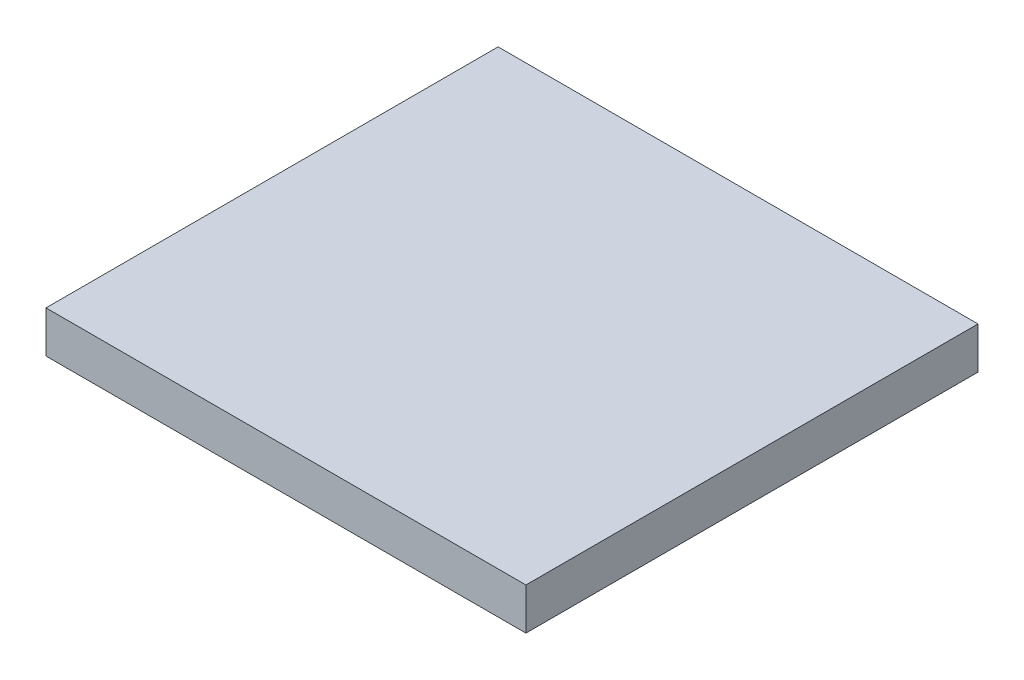
SolidWorks part; units mm, degrees
ref_plane "Front Plane" through (0, 0, 0) normal (0, 0, 1) x (1, 0, 0)
ref_plane "Top Plane" through (0, 0, 0) normal (0, 1, 0) x (1, 0, 0)
ref_plane "Right Plane" through (0, 0, 0) normal (1, 0, 0) x (0, 0, -1)
sketch "Sketch1" plane through (0, 0, 0) normal (0, 1, 0) x (1, 0, 0)
  line L0 (-8.4714, -3.4206) -> (26.0286, -3.4206) construction
  line L1 (26.0286, -3.4206) -> (26.0286, -35.9206) construction
  line L2 (26.0286, -35.9206) -> (-8.4714, -35.9206) construction
  line L3 (-8.4714, -35.9206) -> (-8.4714, -3.4206) construction
  line L4 (-8.4714, -3.4206) -> (26.0286, -3.4206)
  line L5 (26.0286, -3.4206) -> (26.0286, -35.9206)
  line L6 (26.0286, -35.9206) -> (-8.4714, -35.9206)
  line L7 (-8.4714, -35.9206) -> (-8.4714, -3.4206)
extrude "Boss-Extrude1" add sketch "Sketch1" along normal blind 3
